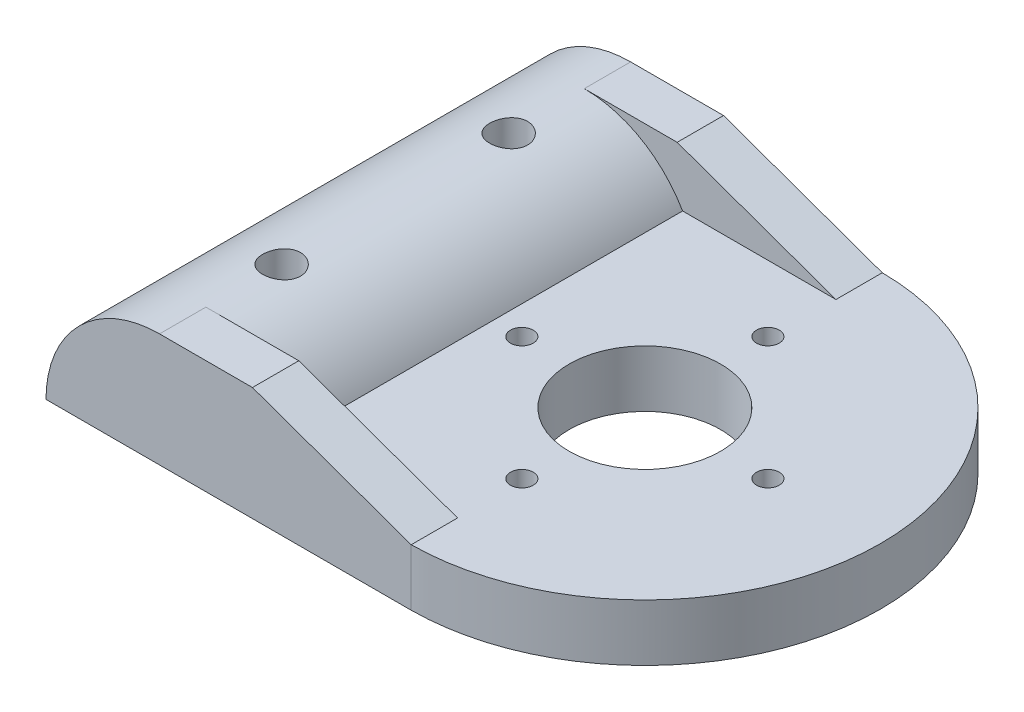
SolidWorks part; units mm, degrees
ref_plane "Alzado" through (0, 0, 0) normal (0, 0, 1) x (1, 0, 0)
ref_plane "Planta" through (0, 0, 0) normal (0, 1, 0) x (1, 0, 0)
ref_plane "Vista lateral" through (0, 0, 0) normal (1, 0, 0) x (0, 0, -1)
sketch "Croquis1" plane through (0, 0, 0) normal (0, 1, 0) x (1, 0, 0)
  line L1 (4.2184, -12.8197) -> (-15.0816, -12.8197)
  line L2 (4.2184, 12.0753) -> (-15.0816, 12.0753)
  line L3 (-15.0816, -12.8197) -> (-15.0816, 12.0753)
  circle A1 centre (4.1184, 6.1284) radius 0.6
  circle A2 centre (4.1192, -0.3722) radius 3.9994
  circle A3 centre (-9.0816, 5.6284) radius 1
  circle A4 centre (-9.0816, -6.3716) radius 1
  circle A5 centre (10.6207, -0.3717) radius 0.6
  circle A6 centre (4.1206, -6.874) radius 0.6
  circle A7 centre (-2.3816, -0.3739) radius 0.6
  arc A8 (4.2184, -12.8197) -> (4.2184, 12.0753) centre (4.1192, -0.3722) ccw
  point P0 (4.2184, 11.9304)
  point P5 (0, 0)
  point P6 (0, 0)
  point P8 (0, 0)
  point P25 (4.1195, -0.3728)
  point P26 (0, 0)
  point P27 (0, 0)
  point P28 (0, 0)
  point P29 (4.1206, -12.8197)
extrude "Saliente-Extruir1" add sketch "Croquis1" along normal blind 3
sketch "Croquis2" plane through (0, 0, 12.8197) normal (0, 0, 1) x (1, 0, 0)
  line L0 (-15.0816, 0) -> (4.2184, 0) construction
  line L1 (-14.2777, 3) -> (-3.8854, 3)
  line L2 (-15.0816, 3) -> (4.2184, 3) construction
  arc A0 (-3.8854, 3) -> (-14.2777, 3) centre (-9.0816, 0) ccw
  dimension "D1" = 12
extrude "Saliente-Extruir2" add sketch "Croquis2" against normal up to surface (24.895 mm away) up to face at (-5.4316, 1.5, -12.0753)
sketch "Croquis3" plane through (0, 3, 0) normal (0, 1, 0) x (1, 0, 0)
  line L0 (-15.0816, 12.0753) -> (-15.0816, -12.8197) construction
  line L1 (4.2184, -12.8197) -> (-9.0816, -12.8197)
  line L2 (4.2184, -12.8197) -> (4.2184, -10.3697)
  line L3 (4.2184, -10.3697) -> (-9.0816, -10.3697)
  line L4 (-9.0816, -12.8197) -> (-9.0816, -10.3697)
  line L5 (4.2184, 12.0753) -> (-9.0816, 12.0753)
  line L6 (4.2184, 12.0753) -> (4.2184, 9.6253)
  line L7 (4.2184, 9.6253) -> (-9.0816, 9.6253)
  line L8 (-9.0816, 12.0753) -> (-9.0816, 9.6253)
  dimension "D1" = 6
  dimension "D2" = 2.45
extrude "Saliente-Extruir3" add sketch "Croquis3" along normal blind 3
sketch "Croquis4" plane through (0, 0, 12.8197) normal (0, 0, 1) x (1, 0, 0)
  line L0 (-4.1716, 6) -> (4.2184, 3)
  line L1 (-9.0816, 6) -> (4.2184, 6) construction
  line L2 (4.2184, 3) -> (4.2184, 6)
  line L3 (4.2184, 6) -> (-4.1716, 6)
  line L4 (-15.0816, 0) -> (4.2184, 0) construction
  line L5 (-15.0816, 0) -> (-16.256, 0)
  line L6 (-9.6833, 5.9698) -> (-9.6833, 7.1492)
  arc A0 (-9.6833, 5.9698) -> (-15.0816, 0) centre (-9.0816, 0) ccw
  arc A1 (-9.6833, 7.1492) -> (-16.256, 0) centre (-9.0816, 0) ccw
  dimension "D2" = 12
  dimension "D1" = 8.39
extrude "Cortar-Extruir1" cut sketch "Croquis4" against normal up to surface (24.895 mm away) up to face at (-5.8956, 3.0995, -12.0753)
sketch "Croquis5" plane through (0, 0, 0) normal (0, -1, 0) x (1, 0, 0)
  circle A0 centre (-9.0816, -5.6284) radius 1 construction
  circle A1 centre (-9.0816, 6.3716) radius 1 construction
  circle A2 centre (-9.0816, -5.6284) radius 1
  circle A3 centre (-9.0816, 6.3716) radius 1
extrude "Cortar-Extruir2" cut sketch "Croquis5" against normal blind 11
